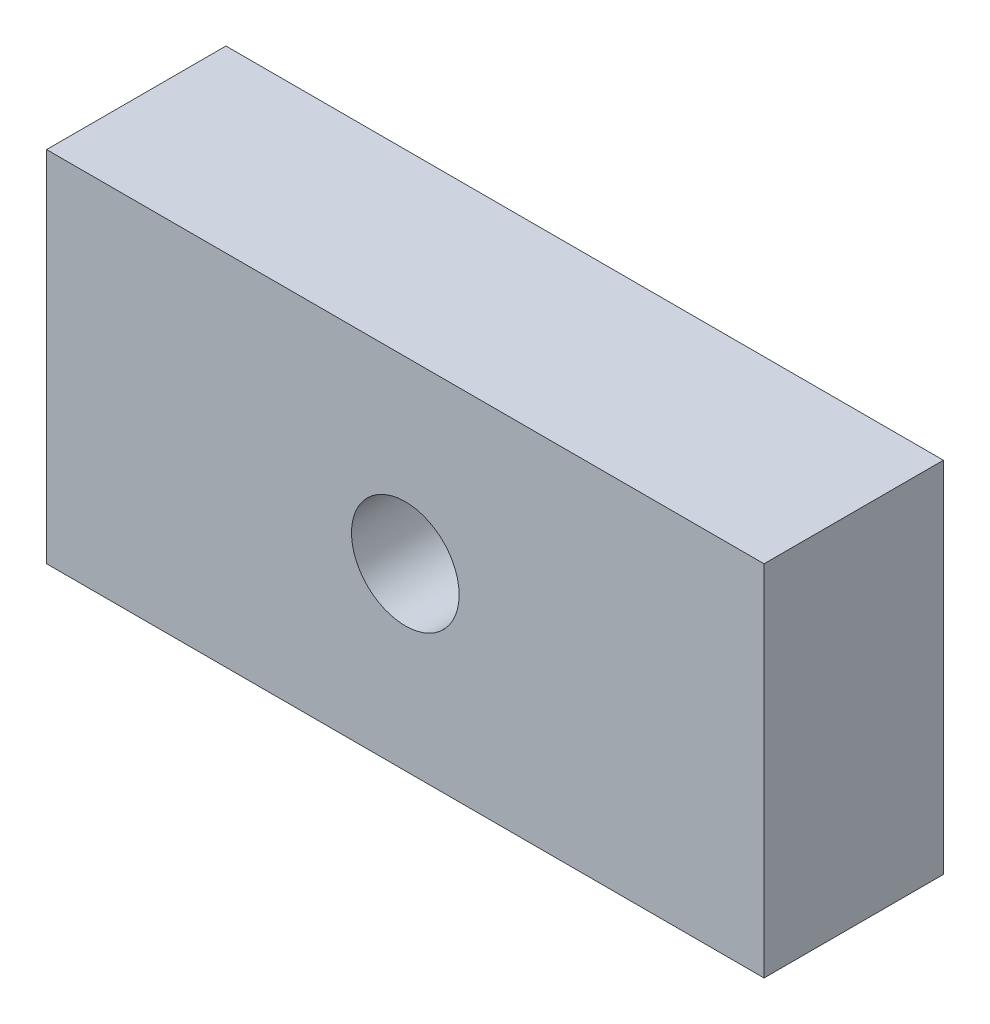
SolidWorks part; units mm, degrees
material "11 500"
ref_plane "Přední rovina" through (0, 0, 0) normal (0, 0, 1) x (1, 0, 0)
ref_plane "Vrchní rovina" through (0, 0, 0) normal (0, 1, 0) x (1, 0, 0)
ref_plane "Pravá rovina" through (0, 0, 0) normal (1, 0, 0) x (0, 0, -1)
sketch "Skica1" plane through (0, 0, 0) normal (0, 0, 1) x (1, 0, 0)
  line L1 (-50, 25) -> (50, 25)
  line L2 (-50, 25) -> (-50, -25)
  line L3 (-50, -25) -> (50, -25)
  line L4 (50, 25) -> (50, -25)
  line L5 (-50, 25) -> (50, -25) construction
  line L6 (-50, -25) -> (50, 25) construction
  point P0 (0, 0)
  dimension "D1" = 100
  dimension "D2" = 50
extrude "Přidat vysunutím1" add sketch "Skica1" along normal blind 25
sketch "Skica2" plane through (0, 0, 25) normal (0, 0, 1) x (1, 0, 0)
  line L0 (-50, 25) -> (-50, -25) construction
  line L1 (50, 25) -> (-50, 25) construction
  circle A0 centre (0, 0) radius 7.5
  point P5 (-50, 0)
  point P8 (0, 25)
  dimension "D1" = 15
extrude "Odebrat vysunutím1" cut sketch "Skica2" against normal up to next contours A0
equation "\"Délka\"= 100mm"
equation "\"D2@Skica1\" = \"Délka\" / 2"
equation "\"D1@Přidat vysunutím1\"= \"Délka\" / 4"
equation "\"D1@Skica1\"= \"Délka\""
equation "\"Odebrat vysunutím1\"= IIF ( \"Délka\" < 60mm , \"suppressed\" , \"unsuppressed\" )"
